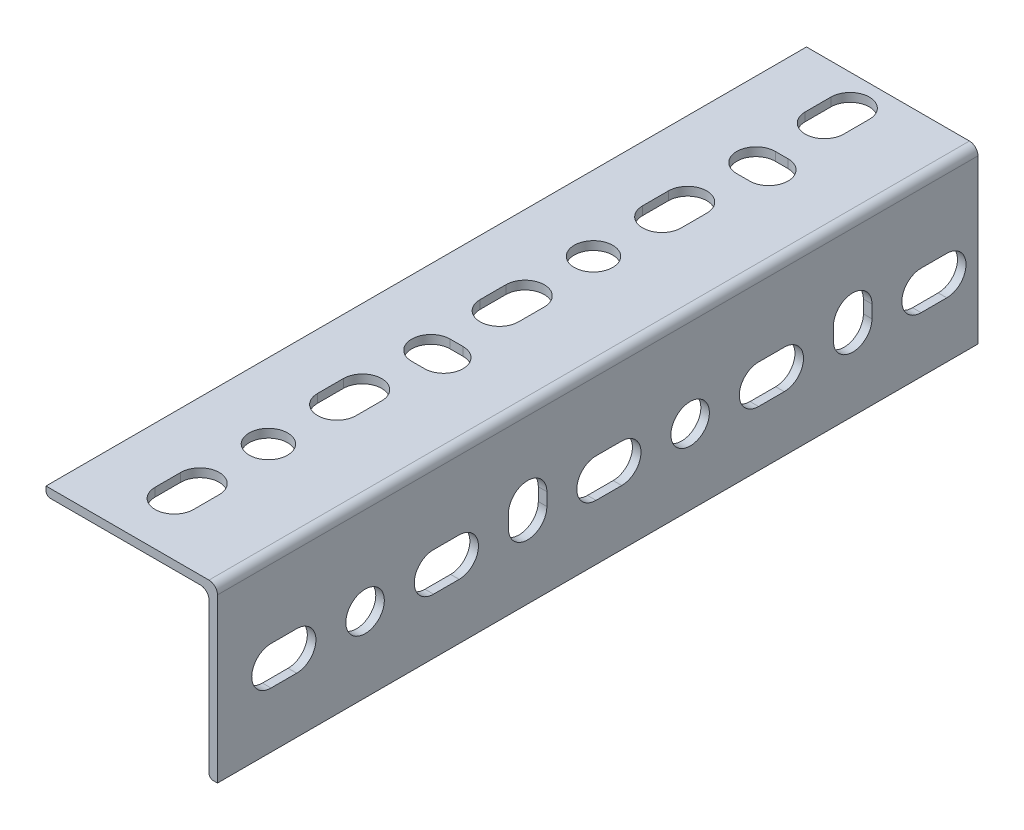
SolidWorks part; units mm, degrees
material "Black Iron Steel"
ref_plane "Front Plane" through (0, 0, 0) normal (0, 0, 1) x (1, 0, 0)
ref_plane "Top Plane" through (0, 0, 0) normal (0, 1, 0) x (1, 0, 0)
ref_plane "Right Plane" through (0, 0, 0) normal (1, 0, 0) x (0, 0, -1)
other "Length"
sketch "Sketch2" plane through (0, 0, 0) normal (0, 1, 0) x (1, 0, 0)
  line L0 (0, 0) -> (0, 177.8)
  dimension "D1" = 177.8
other "Structural Member1"
ref_plane "Plane1" through (0, 0, 0) normal (0, 0, -1) x (-1, 0, 0)
sketch "Sketch13" plane through (0, 0, 0) normal (0, 0, -1) x (-1, 0, 0)
  line L0 (40.1, 0) -> (2, 0)
  line L1 (0, -2) -> (0, -40.1)
  line L2 (39.1, -2) -> (4, -2)
  line L3 (2, -4) -> (2, -39.1)
  line L4 (40.1, 0) -> (40.1, -1)
  line L5 (0, -40.1) -> (1, -40.1)
  arc A0 (40.1, -1) -> (39.1, -2) centre (39.1, -1) cw
  arc A1 (1, -40.1) -> (2, -39.1) centre (1, -39.1) ccw
  arc A2 (4, -2) -> (2, -4) centre (4, -4) ccw
  arc A3 (2, 0) -> (0, -2) centre (2, -2) ccw
  point P2 (21.05, 0)
  point P13 (0, -21.05)
  point P17 (0, 0)
  point P18 (0, 0)
  dimension "r1" = 1
  dimension "r" = 2
  dimension "D1" = 2
  dimension "b" = 40.1
  dimension "d" = 2
sketch "Sketch3" plane through (0, 0, 0) normal (0, 1, 0) x (1, 0, 0)
  line L0 (-22.6, 12.5) -> (-22.6, 18.5) construction
  line L1 (-27.1, 12.5) -> (-27.1, 18.5)
  line L2 (-18.1, 12.5) -> (-18.1, 18.5)
  line L3 (-40.1, 0) -> (-2, 0) construction
  line L4 (-40.1, 177.8) -> (-40.1, 0) construction
  arc A0 (-27.1, 12.5) -> (-18.1, 12.5) centre (-22.6, 12.5) ccw
  arc A1 (-18.1, 18.5) -> (-27.1, 18.5) centre (-22.6, 18.5) ccw
  point P2 (-22.6, 15.5)
  dimension "D1" = 15
  dimension "D3" = 8
  dimension "D2" = 9
  dimension "D4" = 13
extrude "Slot" cut sketch "Sketch3" against normal through all
sketch "Sketch4" plane through (0, 0, 0) normal (0, 1, 0) x (1, 0, 0)
  line L0 (-22.6, 34.5) -> (-22.6, 15.5) construction
  line L1 (-22.6, 12.5) -> (-22.6, 18.5) construction
  circle A0 centre (-22.6, 34.5) radius 4.5
  arc A1 (-18.1, 18.5) -> (-27.1, 18.5) centre (-22.6, 18.5) ccw construction
  dimension "D1" = 7
  dimension "D2" = 9
extrude "Hole" cut sketch "Sketch4" against normal through all
sketch "Sketch14" plane through (0, 0, 0) normal (0, 1, 0) x (1, 0, 0)
  line L0 (-19.6, 72.5) -> (-22.6, 72.5) construction
  line L1 (-19.6, 68) -> (-22.6, 68)
  line L2 (-19.6, 77) -> (-22.6, 77)
  arc A0 (-19.6, 68) -> (-19.6, 77) centre (-19.6, 72.5) ccw
  arc A1 (-22.6, 77) -> (-22.6, 68) centre (-22.6, 72.5) ccw
  point P2 (-21.1, 72.5)
  dimension "D2" = 12
  dimension "D1" = 9
  dimension "D3" = 38
extrude "Vert Slot" cut sketch "Sketch14" against normal through all
pattern_linear "Slot Pattern" count 5 spacing 38 along (0, 0, -1) of "Slot"
pattern_linear "Hole Pattern" count 2 spacing 76 along (0, 0, -1) of "Hole"
pattern_linear "LPattern1" count 2 spacing 76 along (0, 0, -1) of "Vert Slot"
pattern_circular "Other side cuts" count 2 every 90 about axis through (-4, -4, 0) along (0, 0, 1) of "Slot", "Hole", "Vert Slot", "Slot Pattern", "Hole Pattern", "LPattern1"
equation "\"D1@Sketch13\" = \"r@Sketch13\""
